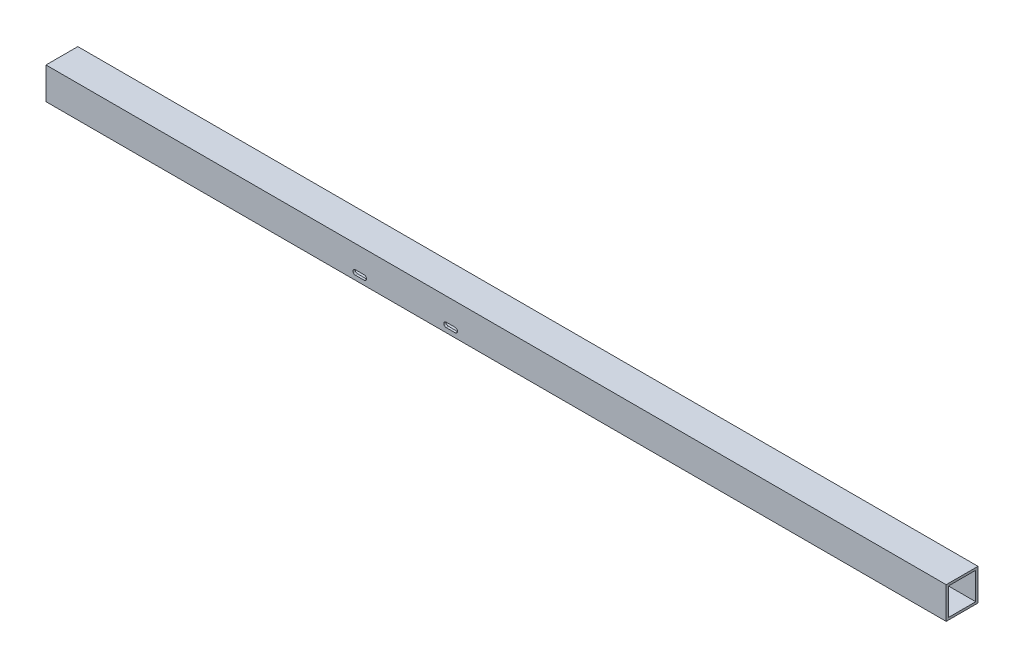
SolidWorks part; units mm, degrees
material "6061 Alloy"
ref_plane "Front Plane" through (0, 0, 0) normal (0, 0, 1) x (1, 0, 0)
ref_plane "Top Plane" through (0, 0, 0) normal (0, 1, 0) x (1, 0, 0)
ref_plane "Right Plane" through (0, 0, 0) normal (1, 0, 0) x (0, 0, -1)
sketch "Sketch1" plane through (0, 0, 0) normal (1, 0, 0) x (0, 0, -1)
  line L0 (41.275, 41.275) -> (3.175, 41.275)
  line L1 (0, 0) -> (44.45, 0)
  line L2 (44.45, 0) -> (44.45, 44.45)
  line L3 (44.45, 44.45) -> (0, 44.45)
  line L4 (0, 44.45) -> (0, 0)
  line L5 (3.175, 41.275) -> (3.175, 3.175)
  line L6 (3.175, 3.175) -> (41.275, 3.175)
  line L7 (41.275, 3.175) -> (41.275, 41.275)
  circle A0 centre (22.225, 22.225) radius 22.225 construction
  dimension "D1" = 44.45
  dimension "D2" = 3.175
extrude "Boss-Extrude1" add sketch "Sketch1" along normal mid plane 1257.3
sketch "Sketch2" plane through (0, 0, 0) normal (0, 0, 1) x (1, 0, 0)
  line L0 (-196.723, 9.525) -> (-184.277, 9.525) construction
  line L1 (-196.723, 12.827) -> (-184.277, 12.827)
  line L2 (-196.723, 6.223) -> (-184.277, 6.223)
  line L3 (-69.723, 9.525) -> (-57.277, 9.525) construction
  line L4 (-69.723, 12.827) -> (-57.277, 12.827)
  line L5 (-69.723, 6.223) -> (-57.277, 6.223)
  line L6 (628.65, 0) -> (-628.65, 0) construction
  arc A0 (-196.723, 12.827) -> (-196.723, 6.223) centre (-196.723, 9.525) ccw
  arc A1 (-184.277, 6.223) -> (-184.277, 12.827) centre (-184.277, 9.525) ccw
  arc A2 (-69.723, 12.827) -> (-69.723, 6.223) centre (-69.723, 9.525) ccw
  arc A3 (-57.277, 6.223) -> (-57.277, 12.827) centre (-57.277, 9.525) ccw
  point P2 (-190.5, 9.525)
  point P7 (-63.5, 9.525)
  point P17 (-177.0674, 15.1365)
  dimension "D3" = 19.05
  dimension "D1" = 63.5
  dimension "D2" = 127
  dimension "D4" = 9.525
  dimension "D5" = 6.604
extrude "Cut-Extrude1" cut sketch "Sketch2" against normal up to next
